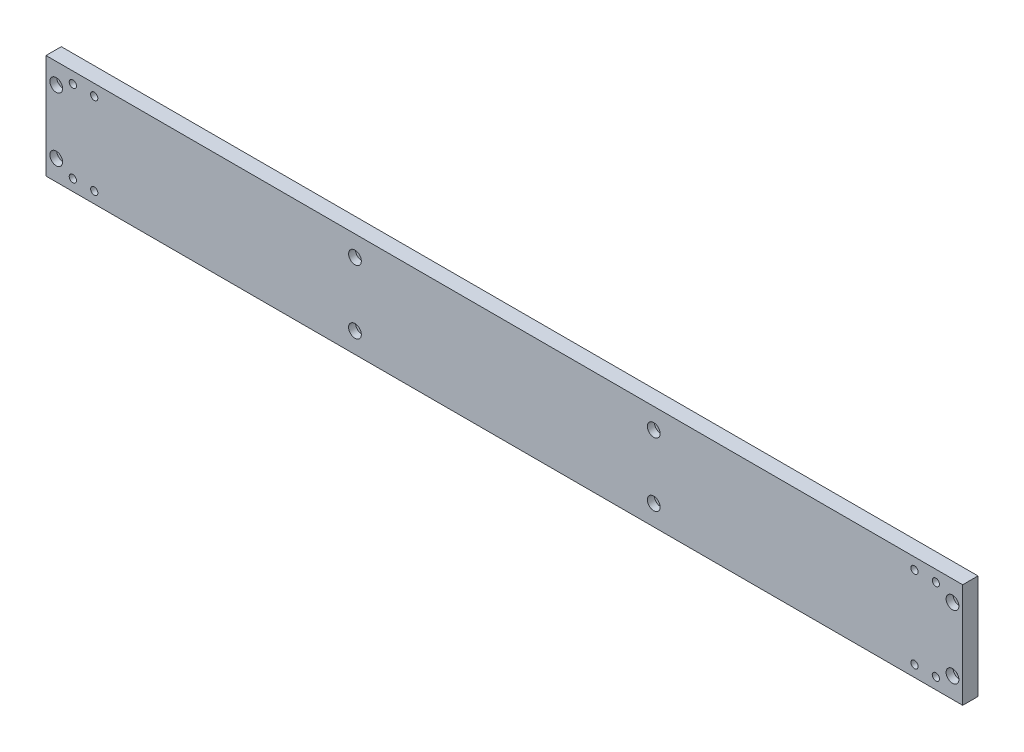
SolidWorks part; units mm, degrees
ref_plane "Plano frontal" through (0, 0, 0) normal (0, 0, 1) x (1, 0, 0)
ref_plane "Plano superior" through (0, 0, 0) normal (0, 1, 0) x (1, 0, 0)
ref_plane "Plano direito" through (0, 0, 0) normal (1, 0, 0) x (0, 0, -1)
ref_plane "Plano1" through (0, 0, 9.525) normal (0, 0, 1) x (1, 0, 0)
sketch "Esboço1" plane through (0, 0, 9.525) normal (0, 0, 1) x (1, 0, 0)
  line L0 (0, 65) -> (0, 0)
  line L1 (0, 0) -> (570.475, 0)
  line L2 (570.475, 0) -> (570.475, 65)
  line L3 (570.475, 65) -> (0, 65)
extrude "Ressalto-extrusão1" add sketch "Esboço1" against normal blind 9.525
hole_wizard "Rebaixo para parafuso de máquina de cabeça sextavada de M41" positions "Esboço3" profile "Esboço2" counterbore size "M4" standard "Ansi Metric"
sketch "Esboço3" plane through (0, 0, 0) normal (0, 0, -1) x (-1, 0, 0)
  point P0 (-30, 7)
  point P1 (-16.7, 7)
  point P2 (-16.7, 58)
  point P3 (-30, 58)
  point P4 (-540.475, 58)
  point P5 (-553.775, 58)
  point P6 (-553.775, 7)
  point P7 (-540.475, 7)
sketch "Esboço2" plane through (30, 7, 0) normal (1, 0, 0) x (0, 1, 0)
  line L0 (0, 0) -> (0, 9.525)
  line L1 (0, 9.525) -> (2.2479, 9.525)
  line L3 (2.2479, 9.525) -> (2.2479, 4.318)
  line L4 (2.2479, 4.318) -> (3.9687, 4.318)
  line L5 (3.9687, 4.318) -> (3.9687, 0)
  line L7 (3.9687, 0) -> (0, 0)
  line L11 (0, -6.35) -> (0, 107.95) construction
  dimension "Thru Hole Dia." = 4.4958
  dimension "Thru Hole Depth" = 9.525
  dimension "C'Bore Dia." = 7.9375
  dimension "C'Bore Depth" = 4.318
hole_wizard "Rebaixo para parafuso de máquina de cabeça sextavada de M42" positions "Esboço5" profile "Esboço4" counterbore size "M4" standard "Ansi Metric"
sketch "Esboço5" plane through (0, 0, 9.525) normal (0, 0, 1) x (1, 0, 0)
  point P0 (6.35, 52.3)
  point P1 (6.35, 12.7)
  point P2 (192.275, 52.3)
  point P3 (192.275, 12.7)
  point P4 (378.2, 52.3)
  point P5 (378.2, 12.7)
  point P6 (564.125, 52.3)
  point P7 (564.125, 12.7)
sketch "Esboço4" plane through (6.35, 52.3, 9.525) normal (1, 0, 0) x (0, -1, 0)
  line L0 (0, 0) -> (0, 9.525)
  line L1 (0, 9.525) -> (2.2479, 9.525)
  line L3 (2.2479, 9.525) -> (2.2479, 4.318)
  line L4 (2.2479, 4.318) -> (3.9687, 4.318)
  line L5 (3.9687, 4.318) -> (3.9687, 0)
  line L7 (3.9687, 0) -> (0, 0)
  line L11 (0, -6.35) -> (0, 107.95) construction
  dimension "Thru Hole Dia." = 4.4958
  dimension "Thru Hole Depth" = 9.525
  dimension "C'Bore Dia." = 7.9375
  dimension "C'Bore Depth" = 4.318
